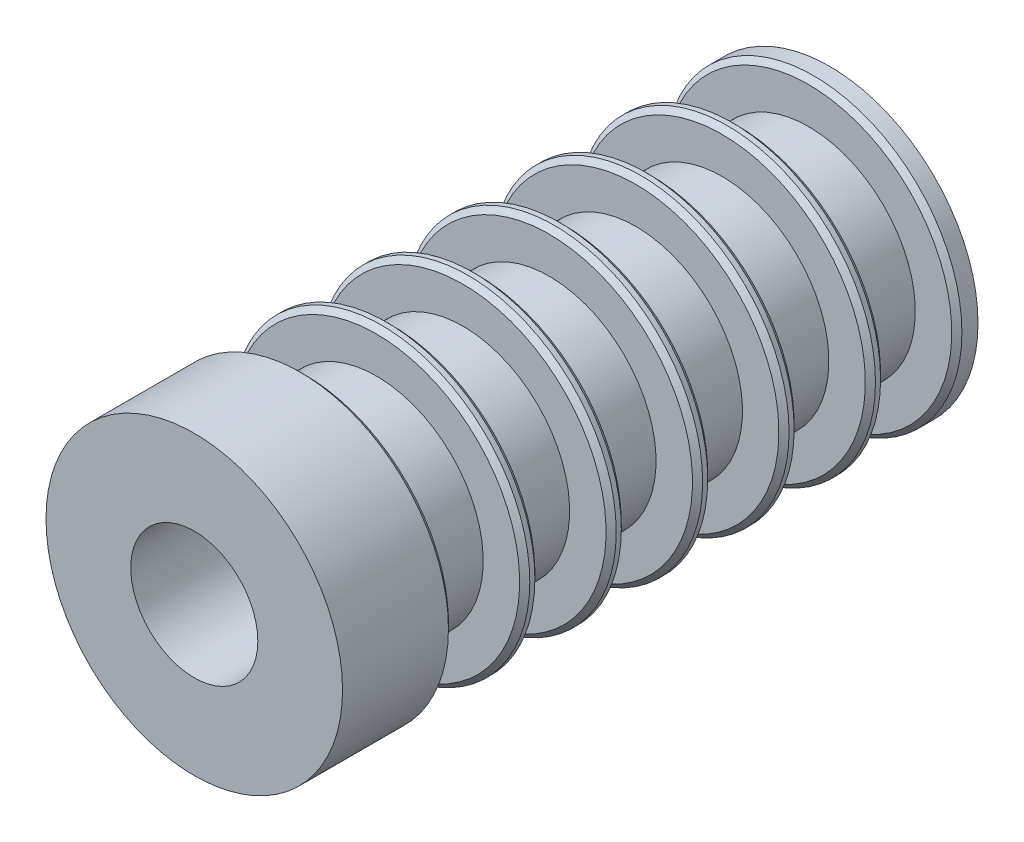
SolidWorks part; units mm, degrees
material "AISI 304"
ref_plane "Front Plane" through (0, 0, 0) normal (0, 0, 1) x (1, 0, 0)
ref_plane "Top Plane" through (0, 0, 0) normal (0, 1, 0) x (1, 0, 0)
ref_plane "Right Plane" through (0, 0, 0) normal (1, 0, 0) x (0, 0, -1)
sketch "Sketch1" plane through (0, 0, 0) normal (0, 0, 1) x (1, 0, 0)
  circle A0 centre (0, 0) radius 11.1125
  circle A1 centre (0, 0) radius 3.2004
  dimension "OD" = 22.225
  dimension "ID" = 6.4008
extrude "Extrude1" add sketch "Sketch1" along normal mid plane 50.8
sketch "Sketch2" plane through (0, 0, 0) normal (1, 0, 0) x (0, 0, -1)
  line L0 (-25.4, -3.2004) -> (25.4, -3.2004) construction
  line L3 (25.4, 3.2004) -> (-25.4, 3.2004) construction
  line L5 (-25.4, -3.2004) -> (25.4, -3.2004)
  line L6 (25.4, 3.2004) -> (-25.4, 3.2004)
sketch "Sketch4" plane through (0, 0, 25.4) normal (0, 0, 1) x (1, 0, 0)
  line L0 (0, 0) -> (-2.263, 2.263)
  line L1 (0, -12.2237) -> (0, 12.2237) construction
  circle A0 centre (0, 0) radius 3.2004 construction
  dimension "D1" = 45
sketch "Sketch5" plane through (0, 0, 25.4) normal (0, 0, 1) x (1, 0, 0)
  circle A0 centre (0, 0) radius 3.2004 construction
  circle A1 centre (0, 0) radius 11.1125
  circle A2 centre (0, 0) radius 11.1125
  circle A3 centre (0, 0) radius 3.2004
  dimension "D1" = 0
extrude "Cut-Extrude1" cut sketch "Sketch5" against normal blind 3.175
sketch "Sketch6" plane through (0, 0, 22.225) normal (0, 0, 1) x (1, 0, 0)
  circle A0 centre (0, 0) radius 4.7625
  dimension "D1" = 9.525
extrude "Cut-Extrude2" cut sketch "Sketch6" against normal through all
sketch "Sketch7" plane through (0, 0, -25.4) normal (0, 0, -1) x (-1, 0, 0)
  circle A0 centre (0, 0) radius 8.001
  circle A1 centre (0, 0) radius 11.1125 construction
  circle A2 centre (0, 0) radius 11.1125
  dimension "D1" = 16.002
extrude "Cut-Extrude3" cut sketch "Sketch7" against normal blind 5.334 from offset 1.5875 offset against normal yes
chamfer "Chamfer2" distance 0.381 angle 45 2 edges at (-11.1125, 0, -23.8125) (-11.1125, 0, -18.4785)
pattern_linear "LPattern1" count 6 spacing 6.477 along (0, 0, 1) of "Cut-Extrude3", "Chamfer2"
